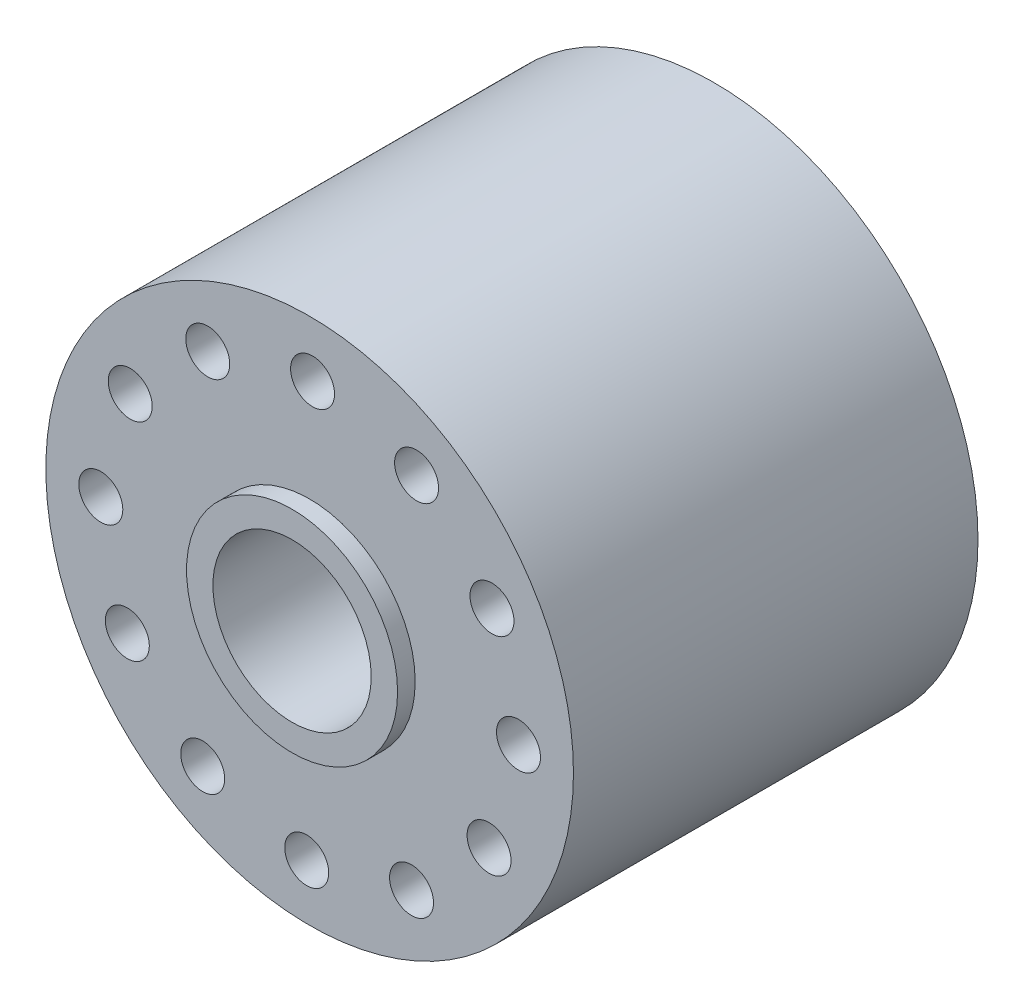
SolidWorks part; units mm, degrees
ref_plane "Front Plane" through (0, 0, 0) normal (0, 0, 1) x (1, 0, 0)
ref_plane "Top Plane" through (0, 0, 0) normal (0, 1, 0) x (1, 0, 0)
ref_plane "Right Plane" through (0, 0, 0) normal (1, 0, 0) x (0, 0, -1)
sketch "Sketch1" plane through (0, 0, 0) normal (0, 0, 1) x (1, 0, 0)
  line L0 (0, 0) -> (0.3308, 23.7477) construction
  line L1 (0, 0) -> (12.1603, 20.4007) construction
  circle A0 centre (0, 0) radius 30
  circle A1 centre (0, 0) radius 12
  circle A14 centre (0.3308, 23.7477) radius 2.5
  circle A15 centre (12.1603, 20.4007) radius 2.5
  circle A16 centre (20.7315, 11.5874) radius 2.5
  circle A17 centre (23.7477, -0.3308) radius 2.5
  circle A18 centre (20.4007, -12.1603) radius 2.5
  circle A19 centre (11.5874, -20.7315) radius 2.5
  circle A20 centre (-0.3308, -23.7477) radius 2.5
  circle A21 centre (-12.1603, -20.4007) radius 2.5
  circle A22 centre (-20.7315, -11.5874) radius 2.5
  circle A23 centre (-23.7477, 0.3308) radius 2.5
  circle A24 centre (-20.4007, 12.1603) radius 2.5
  circle A25 centre (-11.5874, 20.7315) radius 2.5
  point P30 (0, 0)
  dimension "D1" = 30
extrude "Boss-Extrude1" add sketch "Sketch1" along normal mid plane 46
sketch "Sketch2" plane through (0, 0, 0) normal (0, 0, 1) x (1, 0, 0)
  circle A0 centre (0, 0) radius 12
  circle A1 centre (0, 0) radius 9
  dimension "D1" = 24
  dimension "D2" = 18
extrude "Boss-Extrude2" add sketch "Sketch2" along normal mid plane 50
